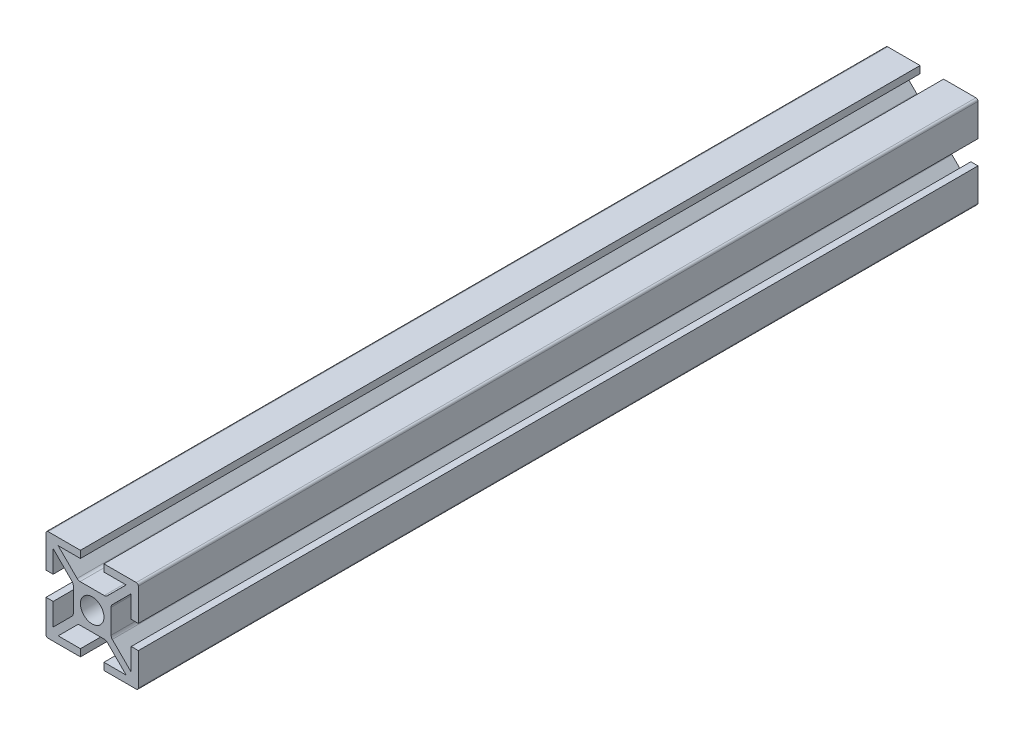
SolidWorks part; units mm, degrees
ref_plane "Plan de face" through (0, 0, 0) normal (0, 0, 1) x (1, 0, 0)
ref_plane "Plan de dessus" through (0, 0, 0) normal (0, 1, 0) x (1, 0, 0)
ref_plane "Plan de droite" through (0, 0, 0) normal (1, 0, 0) x (0, 0, -1)
sketch "Esquisse1" plane through (0, 0, 0) normal (0, 0, 1) x (1, 0, 0)
  line L0 (0, 22) -> (0, -5.6123) construction
  line L1 (-20.8753, 0) -> (5.9514, 0) construction
  line L2 (-2.8, 11) -> (-2.8, 9.3)
  line L3 (-9.3, 2.8) -> (-9.3, 8.0979)
  line L4 (-9.3, 8.0979) -> (-4.5, 3.2979)
  line L5 (-11, 2.8) -> (-11, 11)
  line L6 (-11, 11) -> (-2.8, 11)
  line L7 (-9.3, 2.8) -> (-11, 2.8)
  line L8 (-8.0979, 9.3) -> (-2.8, 9.3)
  line L9 (-8.0979, 9.3) -> (-3.2979, 4.5)
  line L10 (-3.2979, 4.5) -> (3.2979, 4.5)
  line L11 (-4.5, 3.2979) -> (-4.5, -3.2979)
  line L12 (8.0979, 9.3) -> (3.2979, 4.5)
  line L13 (8.0979, 9.3) -> (2.8, 9.3)
  line L14 (2.8, 11) -> (2.8, 9.3)
  line L15 (11, 11) -> (2.8, 11)
  line L16 (11, 2.8) -> (11, 11)
  line L17 (9.3, 2.8) -> (11, 2.8)
  line L18 (9.3, 2.8) -> (9.3, 8.0979)
  line L19 (4.5, 3.2979) -> (4.5, -3.2979)
  line L20 (9.3, 8.0979) -> (4.5, 3.2979)
  line L21 (9.3, -2.8) -> (11, -2.8)
  line L22 (9.3, -8.0979) -> (4.5, -3.2979)
  line L23 (9.3, -2.8) -> (9.3, -8.0979)
  line L24 (11, -2.8) -> (11, -11)
  line L25 (11, -11) -> (2.8, -11)
  line L26 (8.0979, -9.3) -> (3.2979, -4.5)
  line L27 (2.8, -11) -> (2.8, -9.3)
  line L28 (8.0979, -9.3) -> (2.8, -9.3)
  line L29 (-11, -11) -> (-2.8, -11)
  line L30 (-2.8, -11) -> (-2.8, -9.3)
  line L31 (-8.0979, -9.3) -> (-2.8, -9.3)
  line L32 (-3.2979, -4.5) -> (3.2979, -4.5)
  line L33 (-8.0979, -9.3) -> (-3.2979, -4.5)
  line L34 (-9.3, -8.0979) -> (-4.5, -3.2979)
  line L35 (-9.3, -2.8) -> (-9.3, -8.0979)
  line L36 (-9.3, -2.8) -> (-11, -2.8)
  line L37 (-11, -2.8) -> (-11, -11)
  point P17 (0, 4.5)
  point P27 (4.5, 0)
  point P41 (-4.5, 0)
  dimension "D1" = 11
  dimension "D2" = 11
  dimension "D3" = 2.8
  dimension "D4" = 2.8
  dimension "D5" = 1.7
  dimension "D6" = 1.7
  dimension "D7" = 1.7
  dimension "D8" = 1.7
  dimension "D9" = 4.8
  dimension "D10" = 4.8
extrude "Extrusion1" add sketch "Esquisse1" along normal blind 200
sketch "Esquisse2" plane through (0, 0, 0) normal (0, 0, -1) x (-1, 0, 0)
  circle A0 centre (0, 0) radius 2.8
  dimension "D1" = 5.6
extrude "Enlèv. mat.-Extru.1" cut sketch "Esquisse2" against normal through all
fillet "Congé1" radius 0.5 4 edges at (11, -11, 100) (-11, -11, 100) (-11, 11, 100) (11, 11, 100)
fillet "Congé2" radius 1 8 edges at (-4.5, -3.2979, 100) (-4.5, 3.2979, 100) (3.2979, -4.5, 100) (-3.2979, -4.5, 100) (4.5, -3.2979, 100) (4.5, 3.2979, 100) (-3.2979, 4.5, 100) (3.2979, 4.5, 100)
